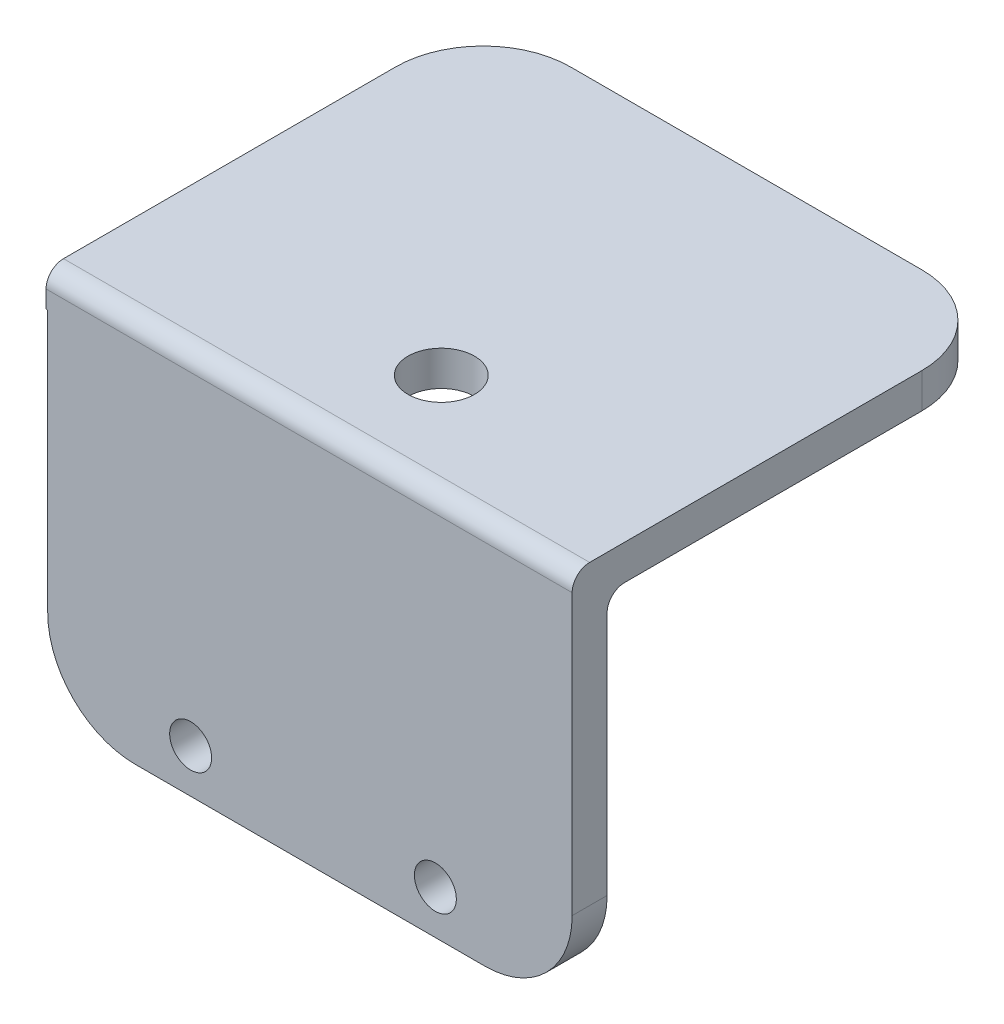
SolidWorks part; units mm, degrees
ref_plane "Front Plane" through (0, 0, 0) normal (0, 0, 1) x (1, 0, 0)
ref_plane "Top Plane" through (0, 0, 0) normal (0, 1, 0) x (1, 0, 0)
ref_plane "Right Plane" through (0, 0, 0) normal (1, 0, 0) x (0, 0, -1)
sketch "Sketch2" plane through (0, 0, 0) normal (0, 0, 1) x (1, 0, 0)
  line L0 (-36.05, 21.6) -> (-3.25, 21.6) construction
  line L1 (2.6247, -0.4) -> (-27.3753, -0.4)
  line L2 (2.6247, -0.4) -> (2.6247, 21.6)
  line L3 (2.6247, 21.6) -> (-27.3753, 21.6)
  line L4 (-27.3753, -0.4) -> (-27.3753, 21.6)
  dimension "D1" = 30
  dimension "D2" = 22
extrude "Boss-Extrude1" add sketch "Sketch2" along normal blind 2
sketch "Sketch3" plane through (0, 21.6, 0) normal (0, 1, 0) x (1, 0, 0)
  line L1 (2.6247, -2) -> (-27.4724, -2)
  line L2 (2.6247, -2) -> (2.6247, 23)
  line L3 (2.6247, 23) -> (-27.4724, 23)
  line L4 (-27.4724, -2) -> (-27.4724, 23)
  dimension "D1" = 25
extrude "Boss-Extrude2" add sketch "Sketch3" against normal blind 2 contours L2 L1 L4 L3
sketch "Sketch4" plane through (0, 0, 2) normal (0, 0, 1) x (1, 0, 0)
  circle A0 centre (-5.2, 2.1) radius 1.2 construction
  circle A1 centre (-5.2, 2.1) radius 1.2
  circle A2 centre (-19.2, 2.1) radius 1.2 construction
  circle A3 centre (-19.2, 2.1) radius 1.2
extrude "Cut-Extrude1" cut sketch "Sketch4" against normal blind 2
fillet "Fillet1" radius 1 1 edges at (-12.3753, 19.6, 0)
fillet "Fillet2" radius 1 1 edges at (-12.4238, 21.6, 2)
fillet "Fillet3" radius 5 2 edges at (2.6247, -0.4, 1) (-27.3753, -0.4, 1)
fillet "Fillet4" radius 5 2 edges at (-27.4724, 20.6, -23) (2.6247, 20.6, -23)
sketch "Sketch5" plane through (0, 21.6, 0) normal (0, 1, 0) x (1, 0, 0)
  circle A0 centre (-10.8906, 4.0277) radius 1.9 construction
  circle A1 centre (-10.8906, 4.0277) radius 1.9
extrude "Cut-Extrude2" cut sketch "Sketch5" against normal blind 2
